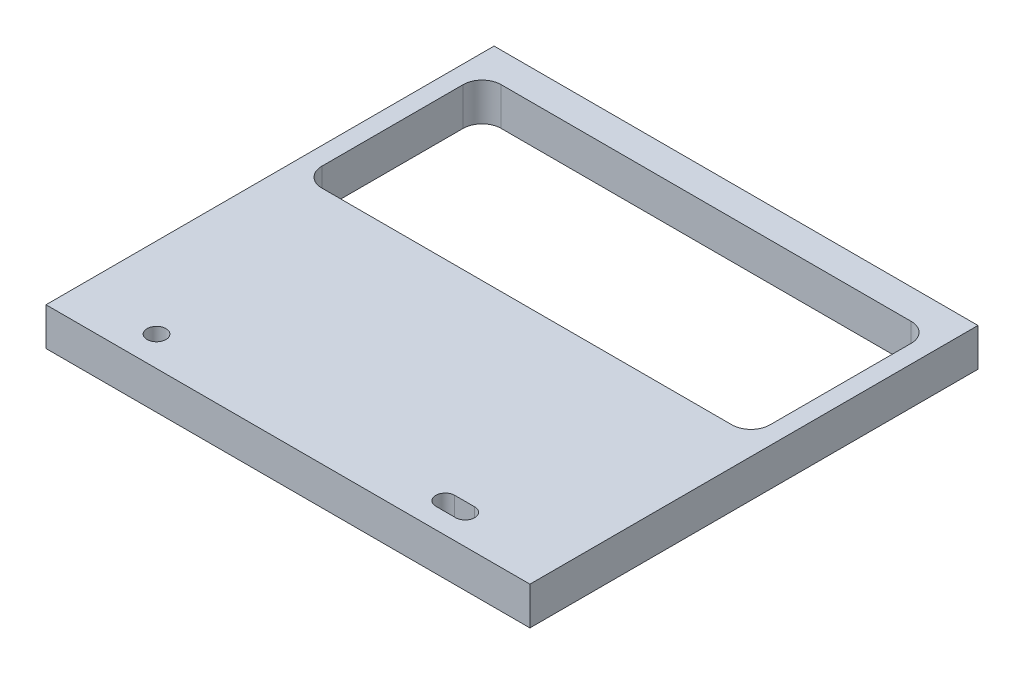
SolidWorks part; units mm, degrees
ref_plane "Front Plane" through (0, 0, 0) normal (0, 0, 1) x (1, 0, 0)
ref_plane "Top Plane" through (0, 0, 0) normal (0, 1, 0) x (1, 0, 0)
ref_plane "Right Plane" through (0, 0, 0) normal (1, 0, 0) x (0, 0, -1)
sketch "Sketch1" plane through (0, 0, 0) normal (0, 1, 0) x (1, 0, 0)
  line L0 (61.83, 5) -> (65.17, 5) construction
  line L1 (0, 0) -> (81, 0)
  line L2 (0, 0) -> (0, 75)
  line L3 (0, 75) -> (81, 75)
  line L4 (81, 0) -> (81, 75)
  line L5 (6.175, 40) -> (74.825, 40)
  line L6 (3, 43.175) -> (3, 66.825)
  line L7 (6.175, 70) -> (74.825, 70)
  line L8 (78, 43.175) -> (78, 66.825)
  line L9 (61.83, 6.585) -> (65.17, 6.585)
  line L10 (61.83, 3.415) -> (65.17, 3.415)
  circle A0 centre (13.5, 5) radius 1.585
  arc A1 (61.83, 6.585) -> (61.83, 3.415) centre (61.83, 5) ccw
  arc A2 (65.17, 3.415) -> (65.17, 6.585) centre (65.17, 5) ccw
  arc A3 (74.825, 70) -> (78, 66.825) centre (74.825, 66.825) cw
  arc A4 (78, 43.175) -> (74.825, 40) centre (74.825, 43.175) cw
  arc A5 (6.175, 40) -> (3, 43.175) centre (6.175, 43.175) cw
  arc A6 (3, 66.825) -> (6.175, 70) centre (6.175, 66.825) cw
  point P13 (63.5, 5)
  dimension "D1" = 3.175
extrude "Boss-Extrude1" add sketch "Sketch1" along normal blind 6.35
